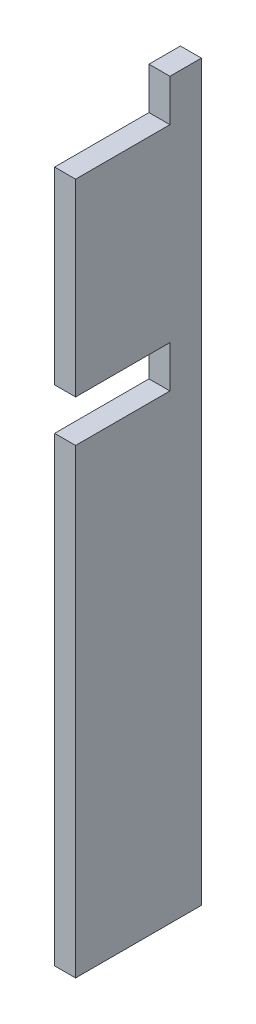
SolidWorks part; units mm, degrees
ref_plane "Front Plane" through (0, 0, 0) normal (0, 0, 1) x (1, 0, 0)
ref_plane "Top Plane" through (0, 0, 0) normal (0, 1, 0) x (1, 0, 0)
ref_plane "Right Plane" through (0, 0, 0) normal (1, 0, 0) x (0, 0, -1)
sketch "Sketch1" plane through (0, 0, 0) normal (1, 0, 0) x (0, 0, -1)
  line L1 (-9.525, 55.5625) -> (9.525, 55.5625)
  line L2 (-9.525, 55.5625) -> (-9.525, -55.5625)
  line L3 (-9.525, -55.5625) -> (9.525, -55.5625)
  line L4 (9.525, 55.5625) -> (9.525, -55.5625)
  line L5 (-9.525, 55.5625) -> (9.525, -55.5625) construction
  line L6 (-9.525, -55.5625) -> (9.525, 55.5625) construction
  point P0 (0, 0)
  dimension "D1" = 111.125
  dimension "D2" = 19.05
extrude "Boss-Extrude1" add sketch "Sketch1" along normal mid plane 3.175
sketch "Sketch2" plane through (1.5875, 0, 0) normal (1, 0, 0) x (0, 0, -1)
  line L0 (-9.525, 55.5625) -> (-9.525, -55.5625) construction
  line L1 (-9.525, 55.5625) -> (4.7625, 55.5625)
  line L2 (-9.525, 55.5625) -> (-9.525, 49.2125)
  line L3 (-9.525, 49.2125) -> (4.7625, 49.2125)
  line L4 (4.7625, 55.5625) -> (4.7625, 49.2125)
  line L5 (-9.525, 20.6375) -> (4.7625, 20.6375)
  line L6 (-9.525, 20.6375) -> (-9.525, 14.2875)
  line L7 (-9.525, 14.2875) -> (4.7625, 14.2875)
  line L8 (4.7625, 20.6375) -> (4.7625, 14.2875)
  line L10 (-9.176, 20.6375) -> (53.9335, 20.6375) construction
  dimension "D1" = 6.35
  dimension "D2" = 14.2875
  dimension "D5" = 6.35
extrude "Cut-Extrude1" cut sketch "Sketch2" against normal through all
